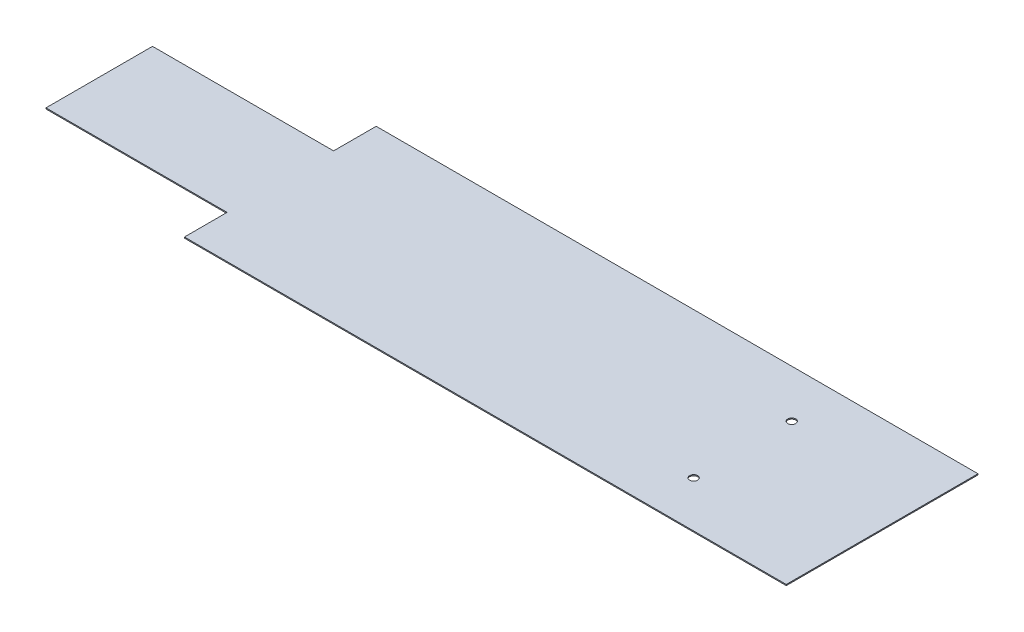
SolidWorks part; units mm, degrees
ref_plane "Front" through (0, 0, 0) normal (0, 0, 1) x (1, 0, 0)
ref_plane "Top" through (0, 0, 0) normal (0, 1, 0) x (1, 0, 0)
ref_plane "Right" through (0, 0, 0) normal (1, 0, 0) x (0, 0, -1)
sketch "Sketch1" plane through (0, 0, 0) normal (0, 1, 0) x (1, 0, 0)
  line L0 (-752.9403, -63.2152) -> (-752.9403, -143.2152)
  line L1 (377.0597, 216.7848) -> (-752.9403, 216.7848)
  line L2 (377.0597, 216.7848) -> (377.0597, -143.2152)
  line L3 (377.0597, -143.2152) -> (-752.9403, -143.2152)
  line L4 (-752.9403, 216.7848) -> (-752.9403, 136.7848)
  line L5 (-752.9403, 136.7848) -> (-1092.9403, 136.7848)
  line L7 (-752.9403, -63.2152) -> (-1092.9403, -63.2152)
  line L8 (-1092.9403, 136.7848) -> (-1092.9403, -63.2152)
  dimension "D1" = 1130
  dimension "D2" = 200
  dimension "D3" = 360
  dimension "D4" = 340
  dimension "D5" = 80
extrude "Boss-Extrude1" add sketch "Sketch1" along normal blind 2
sketch "Sketch2" plane through (0, 2, 0) normal (0, 1, 0) x (1, 0, 0)
  circle A0 centre (116.806, 127.3501) radius 7.5
  circle A1 centre (116.806, -56.884) radius 7.5
  point P4 (116.806, -56.884)
extrude "Cut-Extrude1" cut sketch "Sketch2" against normal blind 2
